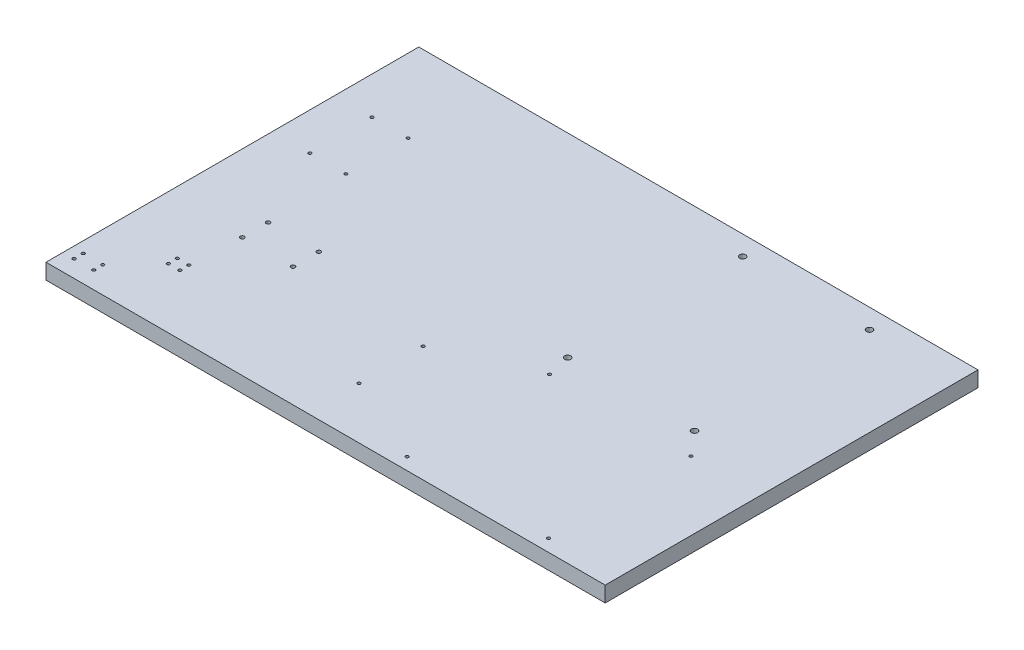
SolidWorks part; units mm, degrees
other "Markup1"
sketch "Sketch12" plane through (370, 12.7, 0) normal (0.2218, 0.7641, 0.6058) x (0.9744, -0.1978, -0.1071)
material "Delrin 2700 NC010, Low Viscosity Acetal Copolymer (SS)"
ref_plane "Front Plane" through (0, 0, 0) normal (0, 0, 1) x (1, 0, 0)
ref_plane "Top Plane" through (0, 0, 0) normal (0, 1, 0) x (1, 0, 0)
ref_plane "Right Plane" through (0, 0, 0) normal (1, 0, 0) x (0, 0, -1)
sketch "Sketch1" plane through (0, 0, 0) normal (0, 1, 0) x (1, 0, 0)
  line L1 (0, 0) -> (457.2, 0)
  line L2 (0, 0) -> (0, 304.8)
  line L3 (0, 304.8) -> (457.2, 304.8)
  line L4 (457.2, 0) -> (457.2, 304.8)
  dimension "D1" = 457.2
  dimension "D2" = 304.8
extrude "Boss-Extrude1" add sketch "Sketch1" along normal blind 12.7
hole_wizard "M3 Tapped Hole1" positions "Sketch2" profile "Sketch3" tap size "M3" standard "AS" end condition through all
sketch "Sketch2" plane through (0, 12.7, 0) normal (0, 1, 0) x (1, 0, 0)
  point P0 (9, 21.4)
  point P3 (25, 21.4)
  point P6 (25, 14)
  point P9 (9, 14)
  point P12 (51, 56.4)
  point P15 (60.4, 56.4)
  point P18 (60.4, 49)
  point P21 (51, 49)
sketch "Sketch3" plane through (9, 12.7, -21.4) normal (1, 0, 0) x (0, 0, 1)
  line L0 (0, 0) -> (0, 12.7)
  line L1 (0, 12.7) -> (1.25, 12.7)
  line L2 (1.25, 12.7) -> (1.25, 0)
  line L5 (1.25, 0) -> (0, 0)
  line L11 (0, -6.35) -> (0, 107.95) construction
  dimension "Thru Tap Drill Dia." = 2.5
  dimension "Thru Tap Drill Depth" = 12.7
cosmetic thread "Hole Thread1"
cosmetic thread "Hole Thread2"
cosmetic thread "Hole Thread3"
cosmetic thread "Hole Thread4"
cosmetic thread "Hole Thread5"
cosmetic thread "Hole Thread6"
cosmetic thread "Hole Thread7"
cosmetic thread "Hole Thread8"
hole_wizard "M3 Tapped Hole2" positions "Sketch4" profile "Sketch5" tap size "M3" standard "AS" end condition through all
sketch "Sketch4" plane through (0, 12.7, 0) normal (0, 1, 0) x (1, 0, 0)
  point P0 (60.125, 235.924)
  point P3 (60.125, 185.124)
  point P6 (30.625, 185.124)
  point P9 (30.625, 235.924)
sketch "Sketch5" plane through (60.125, 12.7, -235.924) normal (1, 0, 0) x (0, 0, 1)
  line L0 (0, 0) -> (0, 12.7)
  line L1 (0, 12.7) -> (1.25, 12.7)
  line L2 (1.25, 12.7) -> (1.25, 0)
  line L5 (1.25, 0) -> (0, 0)
  line L11 (0, -6.35) -> (0, 107.95) construction
  dimension "Thru Tap Drill Dia." = 2.5
  dimension "Thru Tap Drill Depth" = 12.7
cosmetic thread "Hole Thread10"
cosmetic thread "Hole Thread24"
cosmetic thread "Hole Thread30"
cosmetic thread "Hole Thread31"
hole_wizard "M4 Tapped Hole1" positions "Sketch6" profile "Sketch7" tap size "M4" standard "AS" end condition through all
sketch "Sketch6" plane through (0, 12.7, 0) normal (0, 1, 0) x (1, 0, 0)
  point P0 (62.65, 97.8493)
  point P3 (62.65, 118.9493)
  point P6 (104.15, 118.9493)
  point P9 (104.15, 97.8493)
sketch "Sketch7" plane through (62.65, 12.7, -97.8493) normal (1, 0, 0) x (0, 0, 1)
  line L0 (0, 0) -> (0, 12.7)
  line L1 (0, 12.7) -> (1.65, 12.7)
  line L2 (1.65, 12.7) -> (1.65, 0)
  line L5 (1.65, 0) -> (0, 0)
  line L11 (0, -6.35) -> (0, 107.95) construction
  dimension "Thru Tap Drill Dia." = 3.3
  dimension "Thru Tap Drill Depth" = 12.7
cosmetic thread "Hole Thread13"
cosmetic thread "Hole Thread29"
cosmetic thread "Hole Thread38"
cosmetic thread "Hole Thread39"
hole_wizard "M6 Tapped Hole1" positions "Sketch8" profile "Sketch9" tap size "M6" standard "AS" end condition through all
sketch "Sketch8" plane through (0, 12.7, 0) normal (0, 1, 0) x (1, 0, 0)
  point P0 (384.5, 288.8)
  point P3 (280.7782, 288.8)
  point P6 (280.7782, 145.71)
  point P9 (384.5, 145.71)
sketch "Sketch9" plane through (384.5, 12.7, -288.8) normal (1, 0, 0) x (0, 0, 1)
  line L0 (0, 0) -> (0, 12.7)
  line L1 (0, 12.7) -> (2.5, 12.7)
  line L2 (2.5, 12.7) -> (2.5, 0)
  line L5 (2.5, 0) -> (0, 0)
  line L11 (0, -6.35) -> (0, 107.95) construction
  dimension "Thru Tap Drill Dia." = 5
  dimension "Thru Tap Drill Depth" = 12.7
cosmetic thread "Hole Thread17"
cosmetic thread "Hole Thread20"
cosmetic thread "Hole Thread26"
cosmetic thread "Hole Thread27"
hole_wizard "M3 Tapped Hole3" positions "Sketch10" profile "Sketch11" tap size "M3" standard "AS" end condition through all
sketch "Sketch10" plane through (0, 12.7, 0) normal (0, 1, 0) x (1, 0, 0)
  point P0 (213.72, 94.65)
  point P3 (213.72, 42.15)
cosmetic thread "Hole Thread23"
cosmetic thread "Hole Thread33"
sketch "Sketch11" plane through (213.72, 12.7, -94.65) normal (1, 0, 0) x (0, 0, 1)
  line L0 (0, 0) -> (0, 12.7)
  line L1 (0, 12.7) -> (1.25, 12.7)
  line L2 (1.25, 12.7) -> (1.25, 0)
  line L5 (1.25, 0) -> (0, 0)
  line L11 (0, -6.35) -> (0, 107.95) construction
  dimension "Thru Tap Drill Dia." = 2.5
  dimension "Thru Tap Drill Depth" = 12.7
hole_wizard "M3 Tapped Hole4" positions "Sketch13" profile "Sketch14" tap size "M3" standard "AS" end condition through all
sketch "Sketch13" plane through (0, 12.7, 0) normal (0, 1, 0) x (1, 0, 0)
  point P0 (400.9, 10)
  point P3 (285.3, 10)
  point P6 (285.3, 126.425)
  point P9 (400.9, 126.425)
sketch "Sketch14" plane through (400.9, 12.7, -10) normal (1, 0, 0) x (0, 0, 1)
  line L0 (0, 0) -> (0, 12.7)
  line L1 (0, 12.7) -> (1.25, 12.7)
  line L2 (1.25, 12.7) -> (1.25, 0)
  line L5 (1.25, 0) -> (0, 0)
  line L11 (0, -6.35) -> (0, 107.95) construction
  dimension "Thru Tap Drill Dia." = 2.5
  dimension "Thru Tap Drill Depth" = 12.7
cosmetic thread "Hole Thread34"
cosmetic thread "Hole Thread35"
cosmetic thread "Hole Thread36"
cosmetic thread "Hole Thread37"
